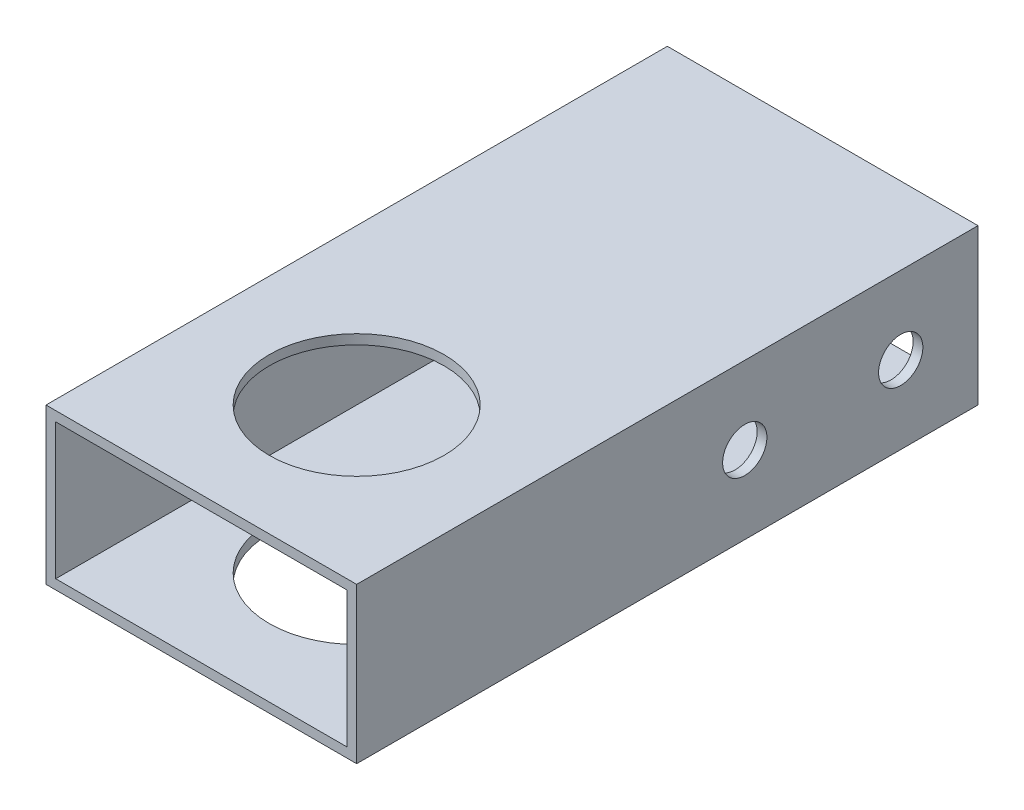
SolidWorks part; units mm, degrees
ref_plane "Front Plane" through (0, 0, 0) normal (0, 0, 1) x (1, 0, 0)
ref_plane "Top Plane" through (0, 0, 0) normal (0, 1, 0) x (1, 0, 0)
ref_plane "Right Plane" through (0, 0, 0) normal (1, 0, 0) x (0, 0, -1)
sketch "Sketch1" plane through (0, 0, 0) normal (0, 0, 1) x (1, 0, 0)
  line L1 (23.8125, -11.1125) -> (-23.8125, -11.1125)
  line L2 (23.8125, -11.1125) -> (23.8125, 11.1125)
  line L3 (23.8125, 11.1125) -> (-23.8125, 11.1125)
  line L4 (-23.8125, -11.1125) -> (-23.8125, 11.1125)
  line L5 (23.8125, -11.1125) -> (-23.8125, 11.1125) construction
  line L6 (23.8125, 11.1125) -> (-23.8125, -11.1125) construction
  line L7 (25.4, -12.7) -> (-25.4, -12.7)
  line L8 (25.4, -12.7) -> (25.4, 12.7)
  line L9 (25.4, 12.7) -> (-25.4, 12.7)
  line L10 (-25.4, -12.7) -> (-25.4, 12.7)
  line L11 (25.4, -12.7) -> (-25.4, 12.7) construction
  line L12 (25.4, 12.7) -> (-25.4, -12.7) construction
  point P0 (0, 0)
  point P6 (0, 0)
  dimension "D1" = 50.8
  dimension "D2" = 25.4
  dimension "D3" = 1.5875
  dimension "D4" = 1.5875
extrude "Boss-Extrude1" add sketch "Sketch1" along normal blind 101.6
sketch "Sketch2" plane through (0, -12.7, 0) normal (0, -1, 0) x (1, 0, 0)
  line L0 (0, 0) -> (0, 76.2) construction
  line L1 (-25.4, 0) -> (25.4, 0) construction
  circle A0 centre (0, 76.2) radius 14.2875
  dimension "D2" = 28.575
  dimension "D1" = 76.2
extrude "Cut-Extrude1" cut sketch "Sketch2" against normal through all
sketch "Sketch3" plane through (25.4, 0, 0) normal (1, 0, 0) x (0, 0, -1)
  line L0 (-34.5186, 0) -> (-16.256, 0)
  line L1 (-9.017, 0) -> (0, 0)
  line L2 (0, -12.7) -> (0, 12.7) construction
  line L3 (-12.6365, 0) -> (-12.6365, 12.7)
  line L4 (-101.6, 12.7) -> (0, 12.7) construction
  line L5 (0, 12.7) -> (0, 0)
  circle A0 centre (-38.1381, 0) radius 3.6195
  circle A3 centre (-12.6365, 0) radius 3.6195
  dimension "D1" = 7.239
  dimension "D2" = 18.2626
  dimension "D3" = 7.239
  dimension "D4" = 9.017
  dimension "D5" = 12.7
extrude "Cut-Extrude2" cut sketch "Sketch3" against normal through all and the other way through all
